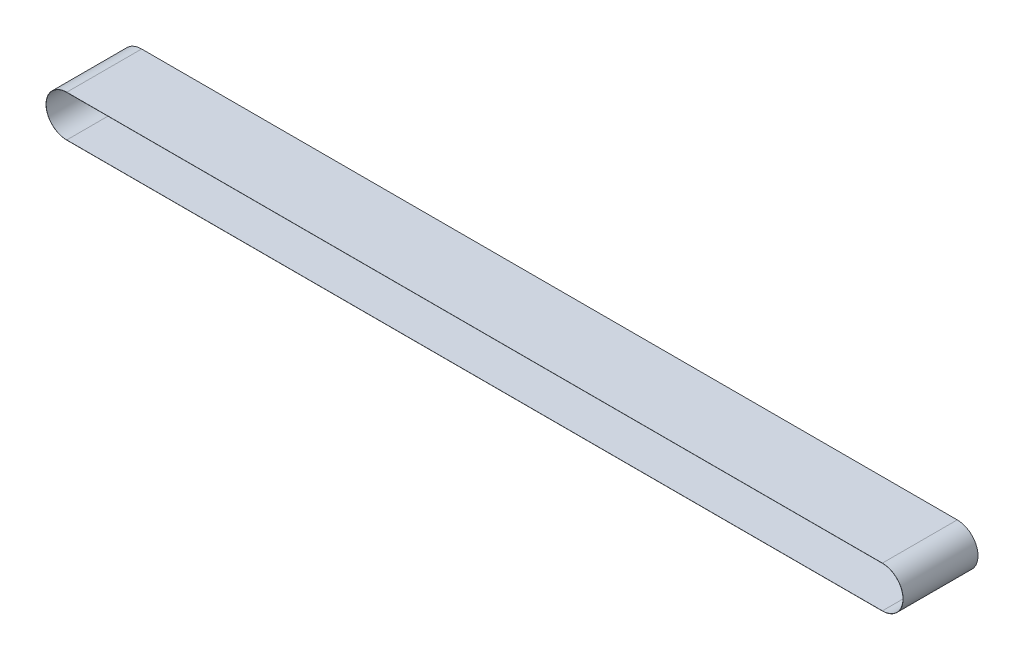
SolidWorks part; units mm, degrees
ref_plane "Plan de face" through (0, 0, 0) normal (0, 0, 1) x (1, 0, 0)
ref_plane "Plan de dessus" through (0, 0, 0) normal (0, 1, 0) x (1, 0, 0)
ref_plane "Plan de droite" through (0, 0, 0) normal (1, 0, 0) x (0, 0, -1)
sketch "Esquisse2" plane through (0, 0, 0) normal (0, 0, 1) x (1, 0, 0)
  line L0 (-2354.4463, 0) -> (115367.8686, 0) construction
  line L1 (0, -2354.4463) -> (0, 115367.8686) construction
  line L3 (-272.3, 13.755) -> (272.3, 13.755)
  line L5 (-272.3, -13.755) -> (272.3, -13.755)
  line L7 (-272.3, 13.755) -> (272.3, -13.755) construction
  line L8 (-272.3, -13.755) -> (272.3, 13.755) construction
  circle A0 centre (0, 0) radius 13.755 construction
  arc A1 (272.3, -13.755) -> (272.3, 13.755) centre (272.3, 0) ccw
  circle A2 centre (272.3, 0) radius 13.755 construction
  arc A3 (-272.3, -13.755) -> (-272.3, 13.755) centre (-272.3, 0) cw
  circle A4 centre (-272.3, 0) radius 13.755 construction
  dimension "D1" = 27.51
  dimension "D4" = 27.51
  dimension "D5" = 27.51
  dimension "D2" = 544.6
  dimension "D3" = 27.51
extrude "Extru.-Mince1" add sketch "Esquisse2" along normal blind 25 and the other way blind 25 thin thin type one direction wall 0.1
equation "\"longueur\"= 650"
equation "\"largeur\"= 50"
equation "\"hauteur\"= 100"
equation "\"d1\"= 20"
equation "\"pied\"= 40"
equation "\"roulement\"= 10"
